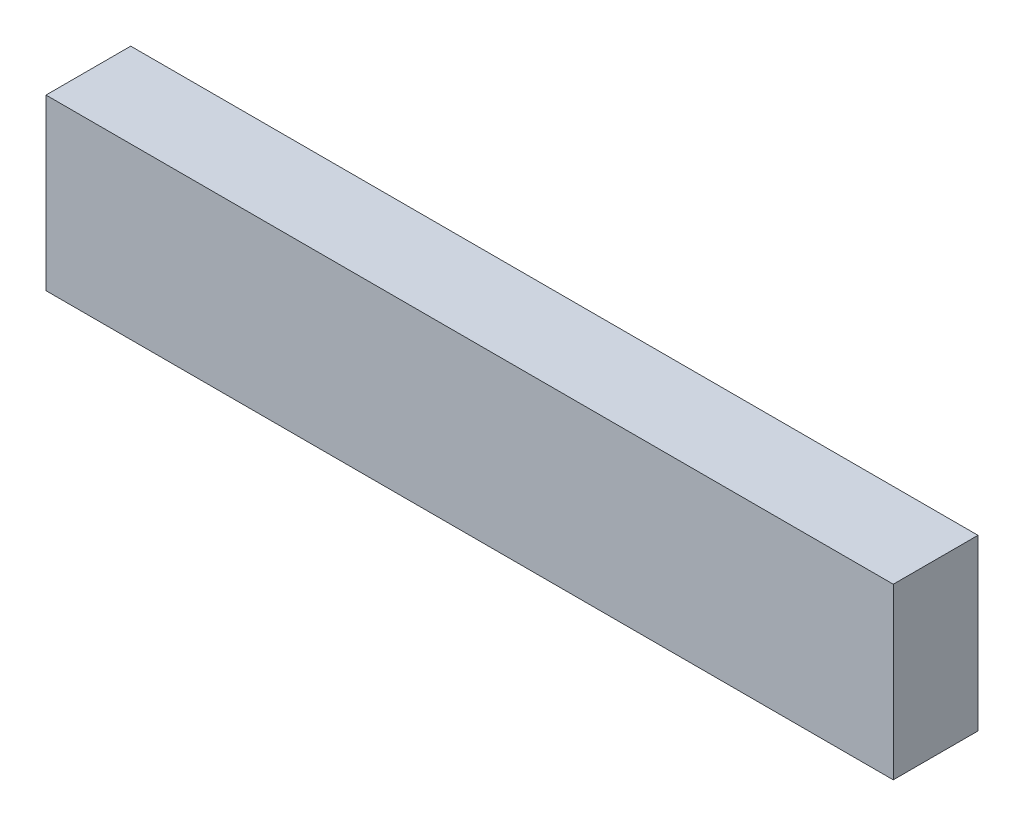
SolidWorks part; units mm, degrees
ref_plane "Front Plane" through (0, 0, 0) normal (0, 0, 1) x (1, 0, 0)
ref_plane "Top Plane" through (0, 0, 0) normal (0, 1, 0) x (1, 0, 0)
ref_plane "Right Plane" through (0, 0, 0) normal (1, 0, 0) x (0, 0, -1)
sketch "Sketch2" plane through (0, 0, 0) normal (0, 0, 1) x (1, 0, 0)
  line L1 (0, 0) -> (50, 0)
  line L2 (0, 0) -> (0, -10)
  line L3 (0, -10) -> (50, -10)
  line L4 (50, 0) -> (50, -10)
extrude "Boss-Extrude1" add sketch "Sketch2" along normal blind 5
